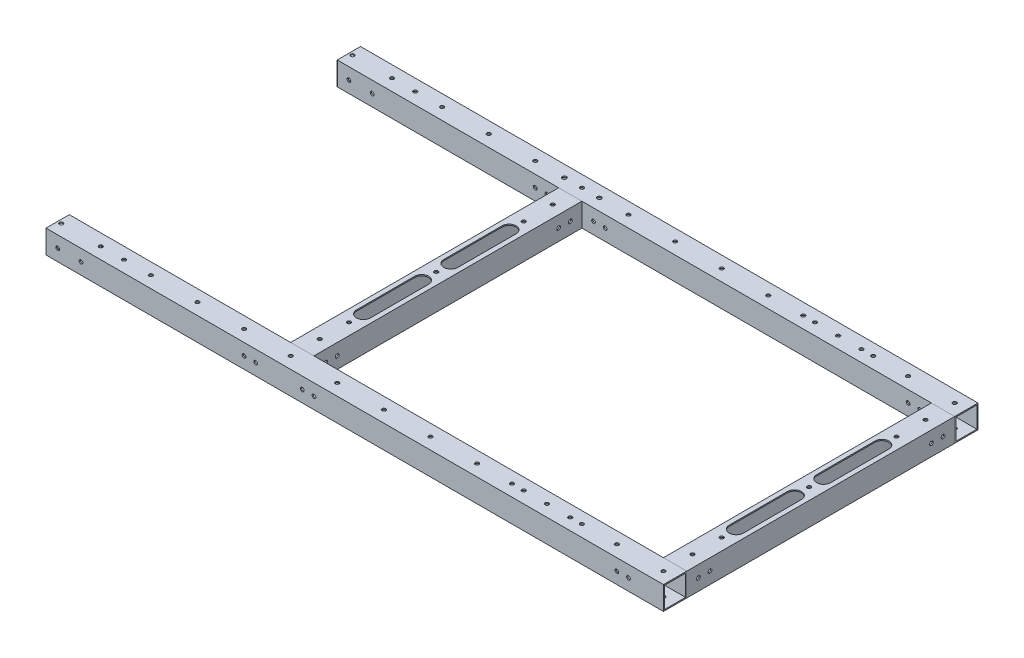
SolidWorks part; units mm, degrees
material "6061 合金"
ref_plane "前视基准面" through (0, 0, 0) normal (0, 0, 1) x (1, 0, 0)
ref_plane "上视基准面" through (0, 0, 0) normal (0, 1, 0) x (1, 0, 0)
ref_plane "右视基准面" through (0, 0, 0) normal (1, 0, 0) x (0, 0, -1)
sketch "草图1" plane through (0, 0, 0) normal (0, 1, 0) x (1, 0, 0)
  line L1 (-285, 125) -> (285, 125)
  line L2 (-285, 125) -> (-285, -125)
  line L3 (-285, -125) -> (285, -125)
  line L4 (285, 125) -> (285, -125)
  line L5 (-285, 125) -> (285, -125) construction
  line L6 (-285, -125) -> (285, 125) construction
  line L7 (-35, 125) -> (-35, -125)
  point P0 (0, 0)
  dimension "D1" = 570
  dimension "D2" = 250
  dimension "D3" = 320
other "铝方管 20X20X1(2)"
ref_plane "基准面1" through (-285, 0, 125) normal (1, 0, 0) x (0, 0, -1)
sketch "草图12" plane through (-285, 0, 125) normal (1, 0, 0) x (0, 0, -1)
  line L1 (-10, -10) -> (10, -10)
  line L2 (-10, -10) -> (-10, 10)
  line L3 (-10, 10) -> (10, 10)
  line L4 (10, -10) -> (10, 10)
  line L5 (-10, -10) -> (10, 10) construction
  line L6 (-10, 10) -> (10, -10) construction
  line L7 (-9, -9) -> (9, -9)
  line L8 (-9, -9) -> (-9, 9)
  line L9 (-9, 9) -> (9, 9)
  line L10 (9, -9) -> (9, 9)
  line L11 (-9, -9) -> (9, 9) construction
  line L12 (-9, 9) -> (9, -9) construction
  point P0 (0, 0)
  point P6 (0, 0)
  point P11 (0, 10)
  point P12 (10, 0)
  point P13 (0, -10)
  point P14 (-10, 0)
  point P15 (0, 0)
  point P16 (0, 0)
  dimension "D1" = 20
  dimension "D2" = 1
  dimension "D3" = 20
sketch "草图13" plane through (0, 10, 0) normal (0, 1, 0) x (1, 0, 0)
  line L0 (-232, 202.1566) -> (-232, -224.1344) construction
  line L1 (-285, 125) -> (-199.9998, 125) construction
  line L2 (-285, 115) -> (-285, 135) construction
  line L3 (-285, -125) -> (-203.686, -125) construction
  line L4 (-285, -135) -> (-285, -115) construction
  line L6 (-285, -115) -> (-285, -135) construction
  circle A0 centre (-232, 125) radius 1.6
  circle A1 centre (-232, -125) radius 1.6
  dimension "D1" = 3.2
  dimension "D2" = 53
extrude "切除-拉伸1" cut sketch "草图13" against normal through all
sketch "草图14" plane through (0, 10, 0) normal (0, 1, 0) x (1, 0, 0)
  line L0 (295, 125) -> (66.8568, 125) construction
  line L1 (295, 135) -> (295, 115) construction
  line L2 (0, 0) -> (394.8072, 0) construction
  line L4 (295, -115) -> (295, 115) construction
  circle A0 centre (185, 125) radius 1.6
  circle A1 centre (185, -125) radius 1.6
  dimension "D1" = 3.2
  dimension "D2" = 110
extrude "切除-拉伸2" cut sketch "草图14" against normal through all and the other way through all
sketch "草图15" plane through (0, 0, 135) normal (0, 0, 1) x (1, 0, 0)
  line L0 (295, 0) -> (-212.7447, 0) construction
  line L1 (295, 10) -> (295, -10) construction
  line L2 (275, 10) -> (275, -10) construction
  line L3 (-25, -10) -> (-25, 10) construction
  line L4 (-45, 10) -> (-45, -10) construction
  circle A0 centre (265, 0) radius 1.6
  circle A1 centre (255, 0) radius 1.6
  circle A2 centre (-15, 0) radius 1.6
  circle A3 centre (-5, 0) radius 1.6
  circle A4 centre (-55, 0) radius 1.6
  circle A5 centre (-65, 0) radius 1.6
  dimension "D1" = 10
  dimension "D2" = 10
  dimension "D3" = 10
  dimension "D4" = 10
  dimension "D5" = 3.2
  dimension "D6" = 10
  dimension "D7" = 10
extrude "切除-拉伸3" cut sketch "草图15" against normal through all
sketch "草图17" plane through (0, 10, 0) normal (0, 1, 0) x (1, 0, 0)
  line L0 (295, -125) -> (-91.519, -125) construction
  line L1 (295, -115) -> (295, -135) construction
  line L2 (327.6682, 0) -> (76.8638, 0) construction
  circle A0 centre (245, -125) radius 1.6
  circle A1 centre (245, 125) radius 1.6
  circle A2 centre (205, 125) radius 1.6
  circle A3 centre (205, -125) radius 1.6
  circle A4 centre (165, 125) radius 1.6
  circle A5 centre (165, -125) radius 1.6
  circle A6 centre (125, 125) radius 1.6
  circle A7 centre (125, -125) radius 1.6
  circle A8 centre (85, 125) radius 1.6
  circle A9 centre (85, -125) radius 1.6
  circle A10 centre (45, 125) radius 1.6
  circle A11 centre (45, -125) radius 1.6
  circle A12 centre (5, 125) radius 1.6
  circle A13 centre (5, -125) radius 1.6
  circle A14 centre (-35, 125) radius 1.6
  circle A15 centre (-35, -125) radius 1.6
  circle A16 centre (-75, 125) radius 1.6
  circle A17 centre (-75, -125) radius 1.6
  circle A18 centre (-115, 125) radius 1.6
  circle A19 centre (-115, -125) radius 1.6
  circle A20 centre (-155, 125) radius 1.6
  circle A21 centre (-155, -125) radius 1.6
  dimension "D2" = 50
  dimension "D3" = 40
  dimension "D4" = 3.2
  dimension "D1" = 11
extrude "切除-拉伸5" cut sketch "草图17" against normal through all
sketch "草图18" plane through (0, 10, 0) normal (0, 1, 0) x (1, 0, 0)
  line L0 (295, -125) -> (-328.2443, -125) construction
  line L1 (295, -115) -> (295, -135) construction
  line L2 (295, 0) -> (140.8565, 0) construction
  line L3 (295, -115) -> (295, 115) construction
  line L4 (285, 115) -> (285, -172.1052) construction
  line L5 (295, 115) -> (275, 115) construction
  line L6 (-35, 115) -> (-35, -172.1052) construction
  line L7 (-25, 115) -> (-45, 115) construction
  line L8 (295, -115) -> (-285, -115) construction
  circle A0 centre (285, -125) radius 1.6
  circle A1 centre (285, -75) radius 1.6
  circle A2 centre (285, 0) radius 1.6
  circle A4 centre (-35, 0) radius 1.6
  circle A5 centre (-35, -75) radius 1.6
  circle A6 centre (-35, 75) radius 1.6
  circle A7 centre (285, 75) radius 1.6
  circle A8 centre (285, 125) radius 1.6
  circle A9 centre (285, -100) radius 1.6
  circle A10 centre (285, 100) radius 1.6
  circle A11 centre (-35, -100) radius 1.6
  circle A12 centre (-35, 100) radius 1.6
  dimension "D1" = 3.2
  dimension "D2" = 50
  dimension "D3" = 50
  dimension "D4" = 15
  dimension "D5" = 15
extrude "切除-拉伸6" cut sketch "草图18" against normal through all
sketch "草图20" plane through (0, 10, 0) normal (0, 1, 0) x (1, 0, 0)
  line L0 (-285, -125) -> (-171.9453, -125) construction
  line L1 (-285, -115) -> (-285, -135) construction
  line L2 (0, 0) -> (-365.8263, 0) construction
  circle A0 centre (-198, -125) radius 1.6
  circle A1 centre (-232, -125) radius 1.6 construction
  circle A2 centre (-198, 125) radius 1.6
  dimension "D1" = 34
  dimension "D2" = 3.2
extrude "切除-拉伸7" cut sketch "草图20" against normal through all
sketch "草图21" plane through (0, 0, 135) normal (0, 0, 1) x (1, 0, 0)
  line L0 (-285, 0) -> (-147.7858, 0) construction
  line L1 (-285, 10) -> (-285, -10) construction
  line L2 (-230.4, 10) -> (-233.6, 10) construction
  line L3 (-230.4, 10) -> (-233.6, 10) construction
  circle A0 centre (-225, 0) radius 1.6
  circle A1 centre (-205, 0) radius 1.6
  point P11 (-232, 10)
  dimension "D1" = 20
  dimension "D2" = 3.2
  dimension "D3" = 7
extrude "切除-拉伸8" cut sketch "草图21" against normal through all
sketch "草图22" plane through (0, 10, 0) normal (0, 1, 0) x (1, 0, 0)
  line L0 (0, 0) -> (-423.6282, 0) construction
  line L1 (-285, -125) -> (-146.9628, -125) construction
  line L2 (-285, -115) -> (-285, -135) construction
  circle A0 centre (-265, -125) radius 1.6
  circle A1 centre (-178, -125) radius 1.6
  circle A2 centre (-198, -125) radius 1.6 construction
  circle A3 centre (-178, 125) radius 1.6
  circle A4 centre (-265, 125) radius 1.6
  dimension "D1" = 3.2
  dimension "D2" = 20
  dimension "D3" = 20
extrude "切除-拉伸9" cut sketch "草图22" against normal through all
sketch "草图23" plane through (0, 10, 0) normal (0, 1, 0) x (1, 0, 0)
  line L0 (0, 0) -> (402.8218, 0) construction
  line L1 (295, -125) -> (53.5405, -125) construction
  line L2 (295, -115) -> (295, -135) construction
  circle A0 centre (155, -125) radius 1.6
  circle A1 centre (215, -125) radius 1.6
  circle A2 centre (165, -125) radius 1.6 construction
  circle A3 centre (205, -125) radius 1.6 construction
  circle A4 centre (215, 125) radius 1.6
  circle A5 centre (155, 125) radius 1.6
  dimension "D1" = 10
  dimension "D2" = 10
  dimension "D3" = 3.2
extrude "切除-拉伸10" cut sketch "草图23" against normal through all
sketch "草图111" plane through (295, 0, 0) normal (1, 0, 0) x (0, 0, -1)
  line L0 (115, 0) -> (-115, 0) construction
  line L1 (115, 10) -> (115, -10) construction
  line L2 (-115, -10) -> (-115, 10) construction
  line L3 (0, 10) -> (0, -10) construction
  line L4 (-115, 10) -> (115, 10) construction
  line L5 (-115, -10) -> (115, -10) construction
  line L6 (115, 10) -> (115, -10) construction
  circle A0 centre (105, 0) radius 1.6
  circle A1 centre (95, 0) radius 1.6
  circle A2 centre (-95, 0) radius 1.6
  circle A3 centre (-105, 0) radius 1.6
  dimension "D1" = 10
  dimension "D2" = 10
  dimension "D3" = 3.2
extrude "切除-拉伸11" cut sketch "草图111" against normal through all
sketch "草图112" plane through (0, 10, 0) normal (0, 1, 0) x (1, 0, 0)
  line L0 (295, -135) -> (-285, -135) construction
  line L1 (-235, -135) -> (-285, -135)
  line L2 (-235, -135) -> (-235, 135)
  line L3 (-235, 135) -> (-285, 135)
  line L4 (-285, -135) -> (-285, 135)
  dimension "D1" = 50
extrude "切除-拉伸12" cut sketch "草图112" against normal blind 20
sketch "草图113" plane through (0, 10, 0) normal (0, 1, 0) x (1, 0, 0)
  line L0 (-35, 75) -> (-35, 0) construction
  line L1 (-35, 62.5) -> (-35, 12.5) construction
  line L2 (-29, 62.5) -> (-29, 12.5)
  line L3 (-41, 62.5) -> (-41, 12.5)
  line L4 (0, 0) -> (-93.6841, 0) construction
  line L5 (-35, -62.5) -> (-35, -12.5) construction
  line L6 (-29, -62.5) -> (-29, -12.5)
  line L7 (-41, -62.5) -> (-41, -12.5)
  line L8 (-35, 75) -> (285, 75) construction
  line L9 (125, 75) -> (125, -88.935) construction
  line L10 (285, -62.5) -> (285, -12.5) construction
  line L11 (279, -62.5) -> (279, -12.5)
  line L12 (291, -62.5) -> (291, -12.5)
  line L13 (285, 62.5) -> (285, 12.5) construction
  line L14 (279, 62.5) -> (279, 12.5)
  line L15 (291, 62.5) -> (291, 12.5)
  arc A0 (-29, 62.5) -> (-41, 62.5) centre (-35, 62.5) ccw
  arc A1 (-41, 12.5) -> (-29, 12.5) centre (-35, 12.5) ccw
  arc A2 (-29, -62.5) -> (-41, -62.5) centre (-35, -62.5) cw
  arc A3 (-41, -12.5) -> (-29, -12.5) centre (-35, -12.5) cw
  arc A4 (279, -62.5) -> (291, -62.5) centre (285, -62.5) ccw
  arc A5 (291, -12.5) -> (279, -12.5) centre (285, -12.5) ccw
  arc A6 (279, 62.5) -> (291, 62.5) centre (285, 62.5) cw
  arc A7 (291, 12.5) -> (279, 12.5) centre (285, 12.5) cw
  point P6 (-35, 37.5)
  point P16 (-35, -37.5)
  point P27 (285, -37.5)
  point P34 (285, 37.5)
  dimension "D1" = 12
  dimension "D2" = 50
extrude "切除-拉伸13" cut sketch "草图113" against normal blind 20
sketch "草图114" plane through (0, 10, 0) normal (0, 1, 0) x (1, 0, 0)
  circle A0 centre (-20, 125) radius 1.75
  circle A1 centre (-50, 125) radius 1.75
extrude "切除-拉伸14" cut sketch "草图114" against normal through all
